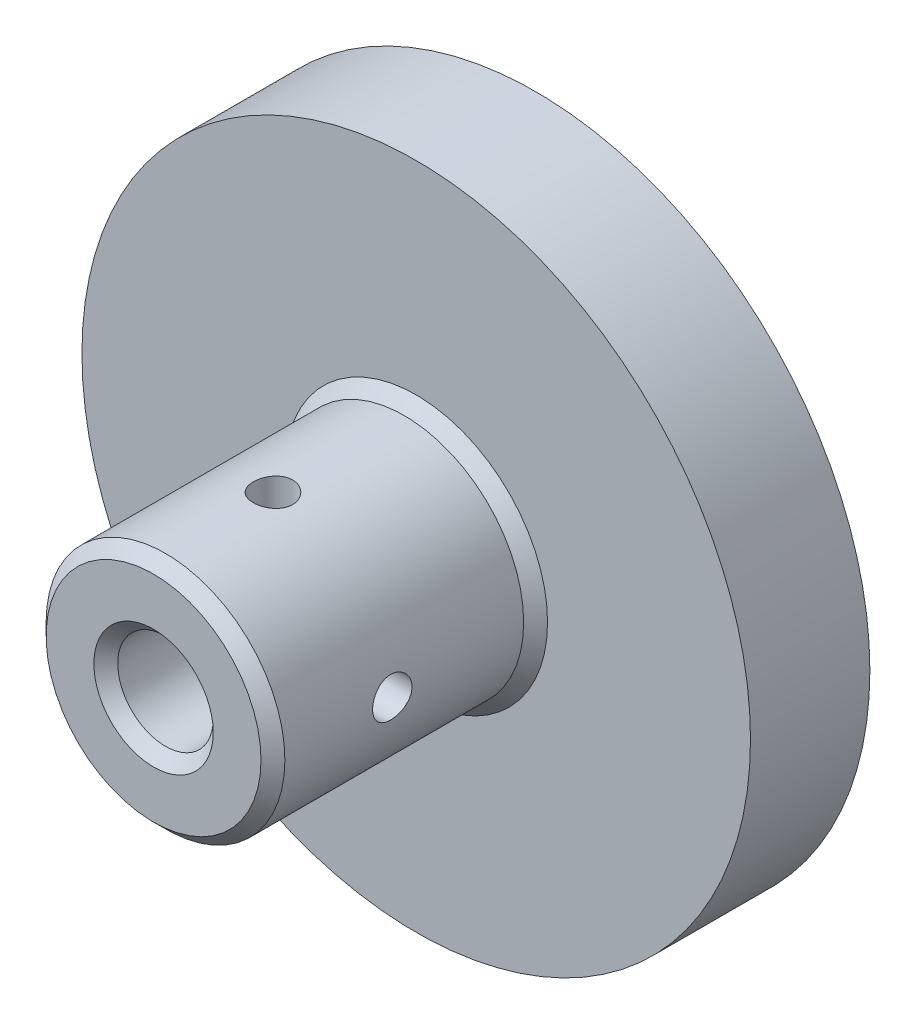
SolidWorks part; units mm, degrees
material "1060 Alloy"
ref_plane "Front Plane" through (0, 0, 0) normal (0, 0, 1) x (1, 0, 0)
ref_plane "Top Plane" through (0, 0, 0) normal (0, 1, 0) x (1, 0, 0)
ref_plane "Right Plane" through (0, 0, 0) normal (1, 0, 0) x (0, 0, -1)
sketch "Sketch1" plane through (0, 0, 0) normal (0, 0, 1) x (1, 0, 0)
  circle A0 centre (0, 0) radius 28
  dimension "D1" = 56
extrude "Boss-Extrude1" add sketch "Sketch1" along normal blind 10
sketch "Sketch2" plane through (0, 0, 10) normal (0, 0, 1) x (1, 0, 0)
  circle A0 centre (0, 0) radius 10
  dimension "D1" = 20
extrude "Boss-Extrude2" add sketch "Sketch2" along normal blind 22
sketch "Sketch4" plane through (0, 0, 32) normal (0, 0, 1) x (1, 0, 0)
  circle A0 centre (0, 0) radius 4
  dimension "D1" = 8
extrude "Cut-Extrude2" cut sketch "Sketch4" against normal through all
chamfer "Chamfer2" distance 1 angle 45 3 edges at (10, 0, 10) (10, 0, 32) (4, 0, 32)
hole_wizard "M4 Tapped Hole1" positions "3DSketch1" profile "Sketch9" tap size "M4" standard "ISO"
sketch3d "3DSketch1"
  line L0 (0, 0, 0) -> (0, 0, 50000) construction
  circle A0 centre (0, 0, 31) radius 10 construction
  point P0 (0, 10, 22)
  point P8 (0, 0, 21)
  dimension "D1" = 10
cosmetic thread "Hole Thread13" parameters "D2"=4
sketch "Sketch9" plane through (0, 10, 22) normal (1, 0, 0) x (0, 0, 1)
  line L0 (0, 0) -> (0, 20)
  line L1 (0, 20) -> (1.65, 20)
  line L2 (1.65, 20) -> (1.65, 0)
  line L5 (1.65, 0) -> (0, 0)
  line L11 (0, -6.35) -> (0, 107.95) construction
  dimension "Thru Tap Drill Dia." = 3.3
  dimension "Thru Tap Drill Depth" = 20
pattern_circular "CirPattern2" count 2 over 90 about axis through (0, 0, 32) along (0, 0, -1) of "M4 Tapped Hole1"
cosmetic thread "Hole Thread14" parameters "D2"=4
